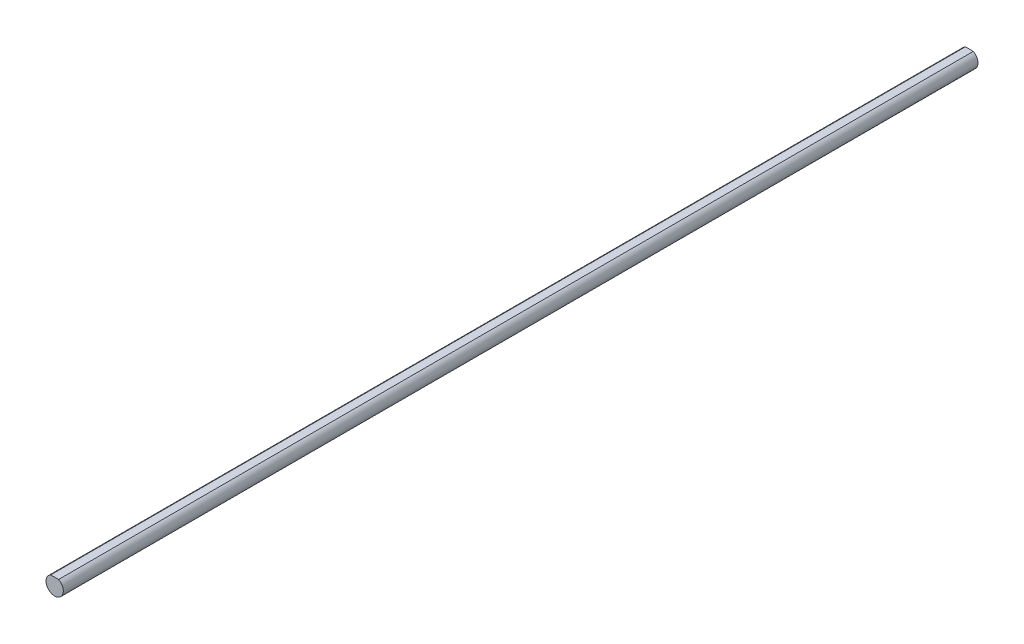
SolidWorks part; units mm, degrees
material "AISI 1020"
ref_plane "Front Plane" through (0, 0, 0) normal (0, 0, 1) x (1, 0, 0)
ref_plane "Top Plane" through (0, 0, 0) normal (0, 1, 0) x (1, 0, 0)
ref_plane "Right Plane" through (0, 0, 0) normal (1, 0, 0) x (0, 0, -1)
ref_plane "Plane1" through (0, 0, -125) normal (0, 0, -1) x (-1, 0, 0)
sketch "Sketch1" plane through (0, 0, -125) normal (0, 0, -1) x (-1, 0, 0)
  line L0 (1.0878, 2.1) -> (-1.0878, 2.1)
  arc A0 (-1.0878, 2.1) -> (1.0878, 2.1) centre (0, 0) ccw
extrude "Boss-Extrude1" add sketch "Sketch1" against normal blind 250
